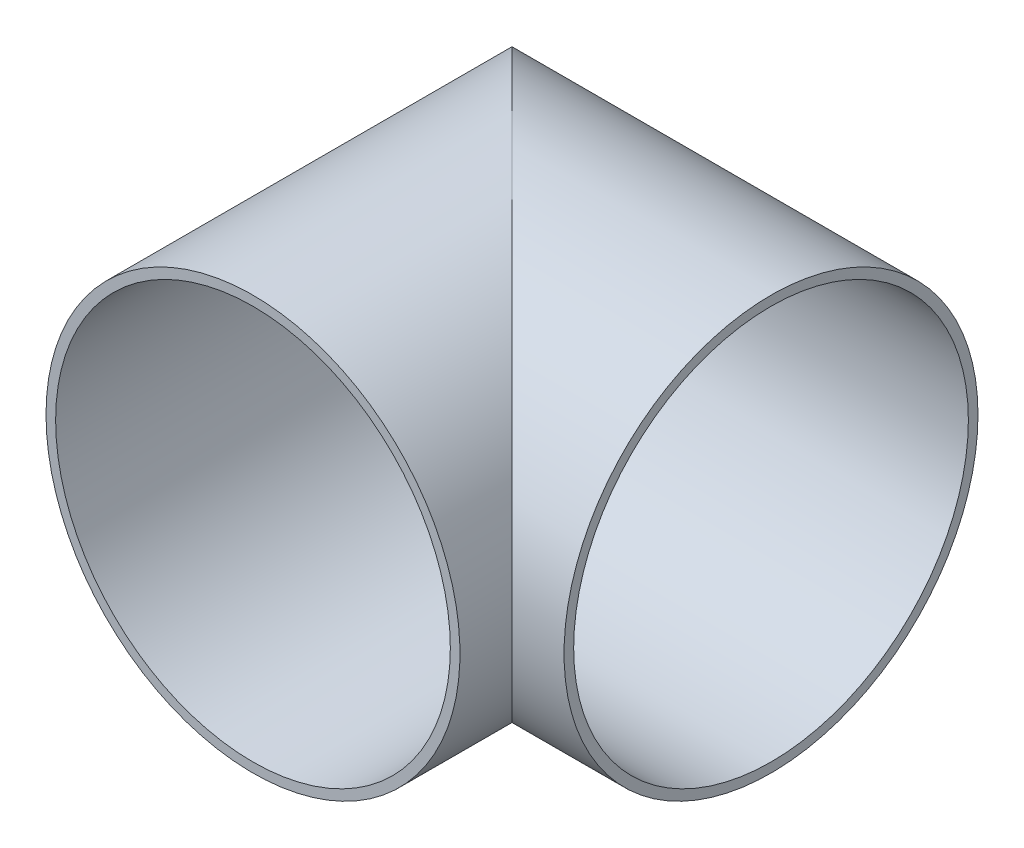
SolidWorks part; units mm, degrees
ref_plane "Front Plane" through (0, 0, 0) normal (0, 0, 1) x (1, 0, 0)
ref_plane "Top Plane" through (0, 0, 0) normal (0, 1, 0) x (1, 0, 0)
ref_plane "Right Plane" through (0, 0, 0) normal (1, 0, 0) x (0, 0, -1)
sketch "Sketch2" plane through (0, 0, 0) normal (0, 1, 0) x (1, 0, 0)
  line L0 (0, -24.4054) -> (0, 8.9321)
  line L1 (0, 8.9321) -> (33.3375, 8.9321)
ref_plane "Plane1" through (33.3375, 0, -8.9321) normal (1, 0, 0) x (0, 0, -1)
sketch "Sketch3" plane through (33.3375, 0, -8.9321) normal (1, 0, 0) x (0, 0, -1)
  circle A0 centre (0, 0) radius 25.4
  circle A1 centre (0, 0) radius 26.6393
sweep "Sweep2" add profiles "Sketch3" path "Sketch2"
